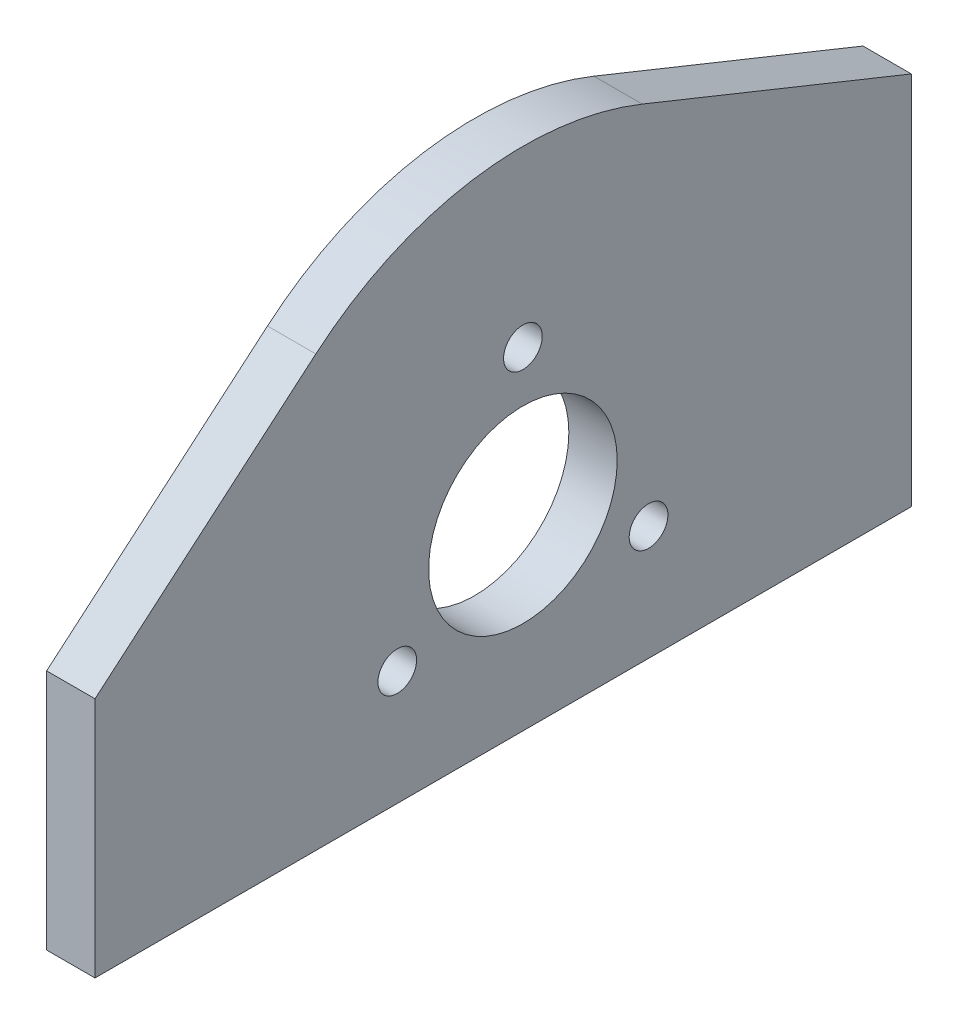
SolidWorks part; units mm, degrees
material "PMMA"
ref_plane "Piano frontale" through (0, 0, 0) normal (0, 0, 1) x (1, 0, 0)
ref_plane "Piano superiore" through (0, 0, 0) normal (0, 1, 0) x (1, 0, 0)
ref_plane "Piano destro" through (0, 0, 0) normal (1, 0, 0) x (0, 0, -1)
sketch "Model" plane through (0, 0, 0) normal (1, 0, 0) x (0, 0, -1)
  line L0 (67.9402, 99.4804) -> (217.5257, 99.4804)
  line L1 (217.5257, 99.4804) -> (217.5258, 94.516)
  line L2 (217.5258, 94.516) -> (67.9406, 94.5157)
  line L3 (67.9406, 94.5157) -> (67.9402, 99.4804)
  line L4 (75.701, 145.6492) -> (169.4508, 145.6492)
  line L5 (169.4508, 145.6492) -> (169.4508, 140.6845)
  line L6 (169.4508, 140.6845) -> (75.7013, 140.6845)
  line L7 (75.7013, 140.6845) -> (75.701, 145.6492)
  line L8 (277.8427, 54.3742) -> (278.3063, 54.3694)
  line L9 (278.3063, 54.3694) -> (7.5827, 54.3742)
  line L10 (-9.9912, 108.2246) -> (89.8382, 182.1486)
  line L11 (107.8333, 184.8972) -> (289.0756, 111.8678)
  line L12 (102.5827, 131.7594) -> (142.5827, 131.7594)
  line L13 (142.5827, 131.7594) -> (142.5827, 101.7594)
  line L14 (142.5827, 101.7594) -> (102.5827, 101.7594)
  line L15 (102.5827, 101.7594) -> (102.5827, 131.7594)
  spline S0 degree 3 poles (11.5524, 84.2317) (11.5524, 82.8135) (10.7957, 81.503) (9.5675, 80.7939) knots 0 0 0 0 1 1 1 1
  spline S1 degree 3 poles (9.5675, 80.7939) (8.3393, 80.0848) (6.8261, 80.0848) (5.5978, 80.7939) knots 0 0 0 0 1 1 1 1
  spline S2 degree 3 poles (5.5978, 80.7939) (4.3696, 81.503) (3.613, 82.8135) (3.613, 84.2317) knots 0 0 0 0 1 1 1 1
  spline S3 degree 3 poles (3.613, 84.2317) (3.613, 85.65) (4.3696, 86.9605) (5.5978, 87.6696) knots 0 0 0 0 1 1 1 1
  spline S4 degree 3 poles (5.5978, 87.6696) (6.8261, 88.3787) (8.3393, 88.3787) (9.5675, 87.6696) knots 0 0 0 0 1 1 1 1
  spline S5 degree 3 poles (9.5675, 87.6696) (10.7957, 86.9605) (11.5524, 85.65) (11.5524, 84.2317) knots 0 0 0 0 1 1 1 1
  spline S6 degree 3 poles (281.5524, 84.2317) (281.5524, 82.8135) (280.7957, 81.503) (279.5675, 80.7939) knots 0 0 0 0 1 1 1 1
  spline S7 degree 3 poles (279.5675, 80.7939) (278.3393, 80.0848) (276.826, 80.0848) (275.5978, 80.7939) knots 0 0 0 0 1 1 1 1
  spline S8 degree 3 poles (275.5978, 80.7939) (274.3696, 81.503) (273.613, 82.8135) (273.613, 84.2317) knots 0 0 0 0 1 1 1 1
  spline S9 degree 3 poles (273.613, 84.2317) (273.613, 85.65) (274.3696, 86.9605) (275.5978, 87.6696) knots 0 0 0 0 1 1 1 1
  spline S10 degree 3 poles (275.5978, 87.6696) (276.826, 88.3787) (278.3393, 88.3787) (279.5675, 87.6696) knots 0 0 0 0 1 1 1 1
  spline S11 degree 3 poles (279.5675, 87.6696) (280.7957, 86.9605) (281.5524, 85.65) (281.5524, 84.2317) knots 0 0 0 0 1 1 1 1
  spline S12 degree 3 poles (106.2634, 174.3826) (109.2777, 172.6422) (111.1346, 169.426) (111.1346, 165.9453) knots 0 0 0 0 1 1 1 1
  spline S13 degree 3 poles (111.1346, 165.9453) (111.1346, 162.4646) (109.2777, 159.2484) (106.2634, 157.508) knots 0 0 0 0 1 1 1 1
  spline S14 degree 3 poles (106.2634, 157.508) (103.249, 155.7677) (99.5352, 155.7677) (96.5208, 157.508) knots 0 0 0 0 1 1 1 1
  spline S15 degree 3 poles (96.5208, 157.508) (93.5065, 159.2484) (91.6496, 162.4646) (91.6496, 165.9453) knots 0 0 0 0 1 1 1 1
  spline S16 degree 3 poles (91.6496, 165.9453) (91.6496, 169.426) (93.5065, 172.6422) (96.5208, 174.3826) knots 0 0 0 0 1 1 1 1
  spline S17 degree 3 poles (96.5208, 174.3826) (99.5352, 176.1229) (103.249, 176.1229) (106.2634, 174.3826) knots 0 0 0 0 1 1 1 1
  spline S18 degree 3 poles (115.181, 160.1104) (115.7944, 159.7563) (116.1722, 159.1018) (116.1722, 158.3936) knots 0 0 0 0 1 1 1 1
  spline S19 degree 3 poles (116.1722, 158.3936) (116.1722, 157.6853) (115.7944, 157.0309) (115.181, 156.6768) knots 0 0 0 0 1 1 1 1
  spline S20 degree 3 poles (115.181, 156.6768) (114.5677, 156.3226) (113.812, 156.3226) (113.1986, 156.6768) knots 0 0 0 0 1 1 1 1
  spline S21 degree 3 poles (113.1986, 156.6768) (112.5852, 157.0309) (112.2074, 157.6853) (112.2074, 158.3936) knots 0 0 0 0 1 1 1 1
  spline S22 degree 3 poles (112.2074, 158.3936) (112.2074, 159.1018) (112.5852, 159.7563) (113.1986, 160.1104) knots 0 0 0 0 1 1 1 1
  spline S23 degree 3 poles (113.1986, 160.1104) (113.812, 160.4645) (114.5677, 160.4645) (115.181, 160.1104) knots 0 0 0 0 1 1 1 1
  spline S24 degree 3 poles (89.6889, 160.1104) (90.3022, 159.7563) (90.6801, 159.1018) (90.6801, 158.3936) knots 0 0 0 0 1 1 1 1
  spline S25 degree 3 poles (90.6801, 158.3936) (90.6801, 157.6853) (90.3022, 157.0309) (89.6889, 156.6768) knots 0 0 0 0 1 1 1 1
  spline S26 degree 3 poles (89.6889, 156.6768) (89.0755, 156.3226) (88.3198, 156.3226) (87.7065, 156.6768) knots 0 0 0 0 1 1 1 1
  spline S27 degree 3 poles (87.7065, 156.6768) (87.0931, 157.0309) (86.7153, 157.6853) (86.7153, 158.3936) knots 0 0 0 0 1 1 1 1
  spline S28 degree 3 poles (86.7153, 158.3936) (86.7153, 159.1018) (87.0931, 159.7563) (87.7065, 160.1104) knots 0 0 0 0 1 1 1 1
  spline S29 degree 3 poles (87.7065, 160.1104) (88.3198, 160.4645) (89.0755, 160.4645) (89.6889, 160.1104) knots 0 0 0 0 1 1 1 1
  spline S30 degree 3 poles (102.4349, 182.1873) (103.0483, 181.8331) (103.4262, 181.1787) (103.4262, 180.4704) knots 0 0 0 0 1 1 1 1
  spline S31 degree 3 poles (103.4262, 180.4704) (103.4262, 179.7622) (103.0483, 179.1077) (102.435, 178.7536) knots 0 0 0 0 1 1 1 1
  spline S32 degree 3 poles (102.435, 178.7536) (101.8216, 178.3995) (101.0659, 178.3995) (100.4525, 178.7536) knots 0 0 0 0 1 1 1 1
  spline S33 degree 3 poles (100.4525, 178.7536) (99.8392, 179.1077) (99.4613, 179.7622) (99.4613, 180.4704) knots 0 0 0 0 1 1 1 1
  spline S34 degree 3 poles (99.4613, 180.4704) (99.4613, 181.1787) (99.8392, 181.8331) (100.4525, 182.1873) knots 0 0 0 0 1 1 1 1
  spline S35 degree 3 poles (100.4525, 182.1873) (101.0659, 182.5414) (101.8216, 182.5414) (102.4349, 182.1873) knots 0 0 0 0 1 1 1 1
  spline S36 degree 3 poles (20.809, 96.941) (20.809, 97.6493) (21.1869, 98.3037) (21.8002, 98.6578) knots 0 0 0 0 1 1 1 1
  spline S37 degree 3 poles (21.8002, 98.6578) (22.4136, 99.012) (23.1693, 99.012) (23.7826, 98.6578) knots 0 0 0 0 1 1 1 1
  spline S38 degree 3 poles (23.7826, 98.6578) (24.396, 98.3037) (24.7739, 97.6493) (24.7739, 96.941) knots 0 0 0 0 1 1 1 1
  spline S39 degree 3 poles (24.7739, 96.941) (24.7739, 96.2328) (24.396, 95.5783) (23.7826, 95.2242) knots 0 0 0 0 1 1 1 1
  spline S40 degree 3 poles (23.7826, 95.2242) (23.1693, 94.8701) (22.4136, 94.8701) (21.8002, 95.2242) knots 0 0 0 0 1 1 1 1
  spline S41 degree 3 poles (21.8002, 95.2242) (21.1869, 95.5783) (20.809, 96.2328) (20.809, 96.941) knots 0 0 0 0 1 1 1 1
  spline S42 degree 3 poles (260.4931, 96.9408) (260.4931, 97.6491) (260.8709, 98.3035) (261.4843, 98.6577) knots 0 0 0 0 1 1 1 1
  spline S43 degree 3 poles (261.4843, 98.6577) (262.0976, 99.0118) (262.8533, 99.0118) (263.4667, 98.6577) knots 0 0 0 0 1 1 1 1
  spline S44 degree 3 poles (263.4667, 98.6577) (264.0801, 98.3035) (264.4579, 97.6491) (264.4579, 96.9408) knots 0 0 0 0 1 1 1 1
  spline S45 degree 3 poles (264.4579, 96.9408) (264.4579, 96.2326) (264.0801, 95.5781) (263.4667, 95.224) knots 0 0 0 0 1 1 1 1
  spline S46 degree 3 poles (263.4667, 95.224) (262.8533, 94.8699) (262.0976, 94.8699) (261.4843, 95.224) knots 0 0 0 0 1 1 1 1
  spline S47 degree 3 poles (261.4843, 95.224) (260.8709, 95.5781) (260.4931, 96.2326) (260.4931, 96.9408) knots 0 0 0 0 1 1 1 1
  spline S48 degree 3 poles (68.2691, 143.1669) (68.2691, 143.8751) (68.6469, 144.5296) (69.2603, 144.8837) knots 0 0 0 0 1 1 1 1
  spline S49 degree 3 poles (69.2603, 144.8837) (69.8737, 145.2378) (70.6294, 145.2378) (71.2427, 144.8837) knots 0 0 0 0 1 1 1 1
  spline S50 degree 3 poles (71.2427, 144.8837) (71.8561, 144.5296) (72.2339, 143.8751) (72.2339, 143.1669) knots 0 0 0 0 1 1 1 1
  spline S51 degree 3 poles (72.2339, 143.1669) (72.2339, 142.4586) (71.8561, 141.8042) (71.2427, 141.45) knots 0 0 0 0 1 1 1 1
  spline S52 degree 3 poles (71.2427, 141.45) (70.6294, 141.0959) (69.8737, 141.0959) (69.2603, 141.45) knots 0 0 0 0 1 1 1 1
  spline S53 degree 3 poles (69.2603, 141.45) (68.6469, 141.8042) (68.2691, 142.4586) (68.2691, 143.1669) knots 0 0 0 0 1 1 1 1
  spline S54 degree 3 poles (172.9986, 143.1669) (172.9986, 143.8751) (173.3764, 144.5296) (173.9898, 144.8837) knots 0 0 0 0 1 1 1 1
  spline S55 degree 3 poles (173.9898, 144.8837) (174.6032, 145.2378) (175.3589, 145.2378) (175.9722, 144.8837) knots 0 0 0 0 1 1 1 1
  spline S56 degree 3 poles (175.9722, 144.8837) (176.5856, 144.5296) (176.9634, 143.8751) (176.9634, 143.1669) knots 0 0 0 0 1 1 1 1
  spline S57 degree 3 poles (176.9634, 143.1669) (176.9634, 142.4586) (176.5856, 141.8042) (175.9722, 141.45) knots 0 0 0 0 1 1 1 1
  spline S58 degree 3 poles (175.9722, 141.45) (175.3589, 141.0959) (174.6032, 141.0959) (173.9898, 141.45) knots 0 0 0 0 1 1 1 1
  spline S59 degree 3 poles (173.9898, 141.45) (173.3764, 141.8042) (172.9986, 142.4586) (172.9986, 143.1669) knots 0 0 0 0 1 1 1 1
  spline S60 degree 3 poles (85.7246, 137.2262) (85.7246, 137.9345) (86.1025, 138.5889) (86.7159, 138.943) knots 0 0 0 0 1 1 1 1
  spline S61 degree 3 poles (86.7159, 138.943) (87.3292, 139.2972) (88.0849, 139.2972) (88.6983, 138.943) knots 0 0 0 0 1 1 1 1
  spline S62 degree 3 poles (88.6983, 138.943) (89.3116, 138.5889) (89.6895, 137.9345) (89.6895, 137.2262) knots 0 0 0 0 1 1 1 1
  spline S63 degree 3 poles (89.6895, 137.2262) (89.6895, 136.518) (89.3116, 135.8635) (88.6983, 135.5094) knots 0 0 0 0 1 1 1 1
  spline S64 degree 3 poles (88.6983, 135.5094) (88.0849, 135.1553) (87.3292, 135.1553) (86.7159, 135.5094) knots 0 0 0 0 1 1 1 1
  spline S65 degree 3 poles (86.7159, 135.5094) (86.1025, 135.8635) (85.7246, 136.518) (85.7246, 137.2262) knots 0 0 0 0 1 1 1 1
  spline S66 degree 3 poles (148.3215, 137.2262) (148.3215, 137.9345) (148.6994, 138.5889) (149.3127, 138.943) knots 0 0 0 0 1 1 1 1
  spline S67 degree 3 poles (149.3127, 138.943) (149.9261, 139.2972) (150.6818, 139.2972) (151.2952, 138.943) knots 0 0 0 0 1 1 1 1
  spline S68 degree 3 poles (151.2952, 138.943) (151.9085, 138.5889) (152.2864, 137.9345) (152.2864, 137.2262) knots 0 0 0 0 1 1 1 1
  spline S69 degree 3 poles (152.2864, 137.2262) (152.2864, 136.518) (151.9085, 135.8635) (151.2952, 135.5094) knots 0 0 0 0 1 1 1 1
  spline S70 degree 3 poles (151.2952, 135.5094) (150.6818, 135.1553) (149.9261, 135.1553) (149.3127, 135.5094) knots 0 0 0 0 1 1 1 1
  spline S71 degree 3 poles (149.3127, 135.5094) (148.6994, 135.8635) (148.3215, 136.518) (148.3215, 137.2262) knots 0 0 0 0 1 1 1 1
  spline S72 degree 3 poles (218.5454, 91.2336) (218.5454, 91.9418) (218.9232, 92.5963) (219.5366, 92.9504) knots 0 0 0 0 1 1 1 1
  spline S73 degree 3 poles (219.5366, 92.9504) (220.15, 93.3045) (220.9057, 93.3045) (221.519, 92.9504) knots 0 0 0 0 1 1 1 1
  spline S74 degree 3 poles (221.519, 92.9504) (222.1324, 92.5963) (222.5102, 91.9418) (222.5102, 91.2336) knots 0 0 0 0 1 1 1 1
  spline S75 degree 3 poles (222.5102, 91.2336) (222.5102, 90.5253) (222.1324, 89.8709) (221.519, 89.5168) knots 0 0 0 0 1 1 1 1
  spline S76 degree 3 poles (221.519, 89.5168) (220.9057, 89.1626) (220.15, 89.1626) (219.5366, 89.5168) knots 0 0 0 0 1 1 1 1
  spline S77 degree 3 poles (219.5366, 89.5168) (218.9232, 89.8709) (218.5454, 90.5253) (218.5454, 91.2336) knots 0 0 0 0 1 1 1 1
  spline S78 degree 3 poles (62.9042, 91.2341) (62.9042, 91.9423) (63.282, 92.5968) (63.8954, 92.9509) knots 0 0 0 0 1 1 1 1
  spline S79 degree 3 poles (63.8954, 92.9509) (64.5088, 93.305) (65.2645, 93.305) (65.8778, 92.9509) knots 0 0 0 0 1 1 1 1
  spline S80 degree 3 poles (65.8778, 92.9509) (66.4912, 92.5968) (66.869, 91.9423) (66.869, 91.2341) knots 0 0 0 0 1 1 1 1
  spline S81 degree 3 poles (66.869, 91.2341) (66.869, 90.5258) (66.4912, 89.8714) (65.8778, 89.5173) knots 0 0 0 0 1 1 1 1
  spline S82 degree 3 poles (65.8778, 89.5173) (65.2645, 89.1631) (64.5088, 89.1631) (63.8954, 89.5173) knots 0 0 0 0 1 1 1 1
  spline S83 degree 3 poles (63.8954, 89.5173) (63.282, 89.8714) (62.9042, 90.5258) (62.9042, 91.2341) knots 0 0 0 0 1 1 1 1
  spline S84 degree 3 poles (169.3736, 91.2336) (169.3736, 91.9418) (169.7514, 92.5963) (170.3648, 92.9504) knots 0 0 0 0 1 1 1 1
  spline S85 degree 3 poles (170.3648, 92.9504) (170.9781, 93.3045) (171.7338, 93.3045) (172.3472, 92.9504) knots 0 0 0 0 1 1 1 1
  spline S86 degree 3 poles (172.3472, 92.9504) (172.9605, 92.5963) (173.3384, 91.9418) (173.3384, 91.2336) knots 0 0 0 0 1 1 1 1
  spline S87 degree 3 poles (173.3384, 91.2336) (173.3384, 90.5253) (172.9605, 89.8709) (172.3472, 89.5168) knots 0 0 0 0 1 1 1 1
  spline S88 degree 3 poles (172.3472, 89.5168) (171.7338, 89.1626) (170.9781, 89.1626) (170.3648, 89.5168) knots 0 0 0 0 1 1 1 1
  spline S89 degree 3 poles (170.3648, 89.5168) (169.7514, 89.8709) (169.3736, 90.5253) (169.3736, 91.2336) knots 0 0 0 0 1 1 1 1
  spline S90 degree 3 poles (112.2515, 91.2336) (112.2515, 91.9418) (112.6293, 92.5963) (113.2427, 92.9504) knots 0 0 0 0 1 1 1 1
  spline S91 degree 3 poles (113.2427, 92.9504) (113.8561, 93.3045) (114.6118, 93.3045) (115.2251, 92.9504) knots 0 0 0 0 1 1 1 1
  spline S92 degree 3 poles (115.2251, 92.9504) (115.8385, 92.5963) (116.2163, 91.9418) (116.2163, 91.2336) knots 0 0 0 0 1 1 1 1
  spline S93 degree 3 poles (116.2163, 91.2336) (116.2163, 90.5253) (115.8385, 89.8709) (115.2251, 89.5168) knots 0 0 0 0 1 1 1 1
  spline S94 degree 3 poles (115.2251, 89.5168) (114.6118, 89.1626) (113.8561, 89.1626) (113.2427, 89.5168) knots 0 0 0 0 1 1 1 1
  spline S95 degree 3 poles (113.2427, 89.5168) (112.6293, 89.8709) (112.2515, 90.5253) (112.2515, 91.2336) knots 0 0 0 0 1 1 1 1
  spline S96 degree 3 poles (289.0756, 111.8678) (292.9178, 110.2369) (296.1347, 108.0507) (298.8362, 105.3491) knots 0 0 0 0 1 1 1 1
  spline S97 degree 3 poles (298.8362, 105.3491) (301.5378, 102.6475) (303.7241, 99.4306) (305.235, 95.8585) knots 0 0 0 0 1 1 1 1
  spline S98 degree 3 poles (305.235, 95.8585) (306.7459, 92.2864) (307.5813, 88.3591) (307.5813, 84.2367) knots 0 0 0 0 1 1 1 1
  spline S99 degree 3 poles (307.5813, 84.2367) (307.5813, 67.7468) (294.2137, 54.3791) (277.8427, 54.3742) knots 0 0 0 0 1 1 1 1
  spline S100 degree 3 poles (7.5827, 54.3742) (-8.766, 54.3791) (-22.1337, 67.7468) (-22.1337, 84.2367) knots 0 0 0 0 1 1 1 1
  spline S101 degree 3 poles (-22.1337, 84.2367) (-22.1337, 92.4816) (-18.7918, 99.946) (-13.3886, 105.3491) knots 0 0 0 0 1 1 1 1
  spline S102 degree 3 poles (-13.3886, 105.3491) (-12.0378, 106.6999) (-10.5582, 107.9219) (-9.9912, 108.2246) knots 0 0 0 0 1 1 1 1
  spline S103 degree 3 poles (89.8382, 182.1486) (90.5198, 182.6635) (91.6227, 183.3375) (92.7755, 183.8987) knots 0 0 0 0 1 1 1 1
  spline S104 degree 3 poles (92.7755, 183.8987) (93.9282, 184.4598) (95.1308, 184.9082) (96.3649, 185.2389) knots 0 0 0 0 1 1 1 1
  spline S105 degree 3 poles (96.3649, 185.2389) (97.5989, 185.5696) (98.8646, 185.7825) (100.1435, 185.8729) knots 0 0 0 0 1 1 1 1
  spline S106 degree 3 poles (100.1435, 185.8729) (101.4224, 185.9633) (102.7145, 185.9311) (104.0017, 185.7714) knots 0 0 0 0 1 1 1 1
  spline S107 degree 3 poles (104.0017, 185.7714) (105.2888, 185.6116) (106.5709, 185.3244) (107.8333, 184.8972) knots 0 0 0 0 1 1 1 1
sketch "Schizzo5" plane through (0, 0, 0) normal (1, 0, 0) x (0, 0, -1)
  line L0 (-95, 0) -> (201, 0) construction
  line L1 (0, 81) -> (0, 0) construction
  dimension "D1" = 95
  dimension "D2" = 201
  dimension "D3" = 81
sketch "Schizzo2" plane through (0, 0, 0) normal (1, 0, 0) x (0, 0, -1)
  line L0 (0, 81) -> (-42.1808, 56.6469) construction
  line L1 (0, 81) -> (0, 129.7062) construction
  line L2 (0, 81) -> (42.1808, 56.6469) construction
  line L4 (0, 81) -> (0, 0) construction
  circle A0 centre (-95, 0) radius 4
  circle A1 centre (201, 0) radius 4
  circle A2 centre (12.9904, 73.5) radius 2
  circle A3 centre (-12.9904, 73.5) radius 2
  circle A4 centre (0, 96) radius 2
  circle A5 centre (0, 81) radius 15 construction
  circle A6 centre (0, 81) radius 9.75
  circle A7 centre (0, 81) radius 20.25 construction
  circle A8 centre (0, 81) radius 17.5 construction
  point P15 (0, 96)
  point P16 (12.9904, 73.5)
  point P17 (-12.9904, 73.5)
  dimension "D1" = 8
  dimension "D3" = 4
  dimension "D4" = 30
  dimension "D7" = 19.5
  dimension "D10" = 40.5
  dimension "D11" = 35
  dimension "D5" = 120
  dimension "D6" = 120
sketch "Schizzo3" plane through (0, 0, 0) normal (1, 0, 0) x (0, 0, -1)
  line L0 (40.1602, 61.6471) -> (40.1602, 100.3948)
  line L1 (213.3346, 30.6081) -> (12.3346, 111.6081) construction
  line L3 (-44.2392, 86.6471) -> (-21.4107, 106.1114)
  line L4 (40.1602, 100.3948) -> (12.3346, 111.6081)
  line L8 (-44.2392, 86.6471) -> (-44.2392, 61.6471)
  line L10 (-44.2392, 61.6471) -> (40.1602, 61.6471)
  arc A0 (12.3346, 111.6081) -> (-21.4107, 106.1114) centre (0, 81) ccw
  dimension "D3" = 30
  dimension "D14" = 30
  dimension "D15" = 25
extrude "Estrusione-Estrusione1" add sketch "Schizzo3" along normal blind 5
extrude "Taglio-Estrusione1" cut sketch "Schizzo2" along normal through all
equation "\"Thickness\"=5"
equation "\"D1@Estrusione-Estrusione1\"=\"Thickness\""
